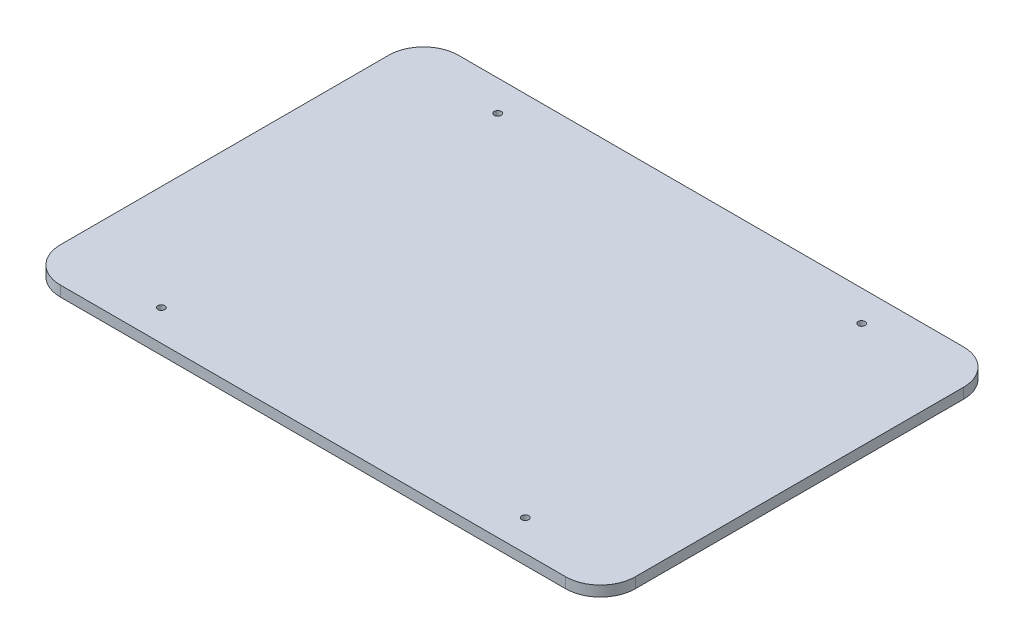
SolidWorks part; units mm, degrees
ref_plane "Front Plane" through (0, 0, 0) normal (0, 0, 1) x (1, 0, 0)
ref_plane "Top Plane" through (0, 0, 0) normal (0, 1, 0) x (1, 0, 0)
ref_plane "Right Plane" through (0, 0, 0) normal (1, 0, 0) x (0, 0, -1)
sketch "Sketch1" plane through (0, 0, 0) normal (0, 1, 0) x (1, 0, 0)
  line L1 (-82.55, 57.15) -> (82.55, 57.15)
  line L2 (-82.55, 57.15) -> (-82.55, -57.15)
  line L3 (-82.55, -57.15) -> (82.55, -57.15)
  line L4 (82.55, 57.15) -> (82.55, -57.15)
  line L5 (-82.55, 57.15) -> (82.55, -57.15) construction
  line L6 (-82.55, -57.15) -> (82.55, 57.15) construction
  point P0 (0, 0)
  dimension "D1" = 165.1
  dimension "D2" = 114.3
extrude "Boss-Extrude1" add sketch "Sketch1" along normal blind 3
fillet "Fillet1" radius 10 4 edges at (82.55, 1.5, 57.15) (82.55, 1.5, -57.15) (-82.55, 1.5, -57.15) (-82.55, 1.5, 57.15)
sketch "Sketch2" plane through (0, 0, 0) normal (0, -1, 0) x (1, 0, 0)
  line L4 (82.55, -47.15) -> (82.55, 47.15)
  line L5 (72.55, 57.15) -> (-72.55, 57.15)
  line L6 (-82.55, 47.15) -> (-82.55, -47.15)
  line L7 (-72.55, -57.15) -> (72.55, -57.15)
  line L8 (82.55, -47.15) -> (82.55, 47.15)
  line L9 (72.55, 57.15) -> (-72.55, 57.15)
  line L10 (-82.55, 47.15) -> (-82.55, -47.15)
  line L11 (-72.55, -57.15) -> (72.55, -57.15)
  circle A0 centre (-52.43, 48.26) radius 1 construction
  circle A1 centre (52.07, 48.26) radius 1 construction
  circle A2 centre (-52.43, -48.34) radius 1 construction
  circle A3 centre (52.07, -48.34) radius 1 construction
  arc A4 (82.55, 47.15) -> (72.55, 57.15) centre (72.55, 47.15) ccw
  arc A5 (-72.55, 57.15) -> (-82.55, 47.15) centre (-72.55, 47.15) ccw
  arc A6 (-82.55, -47.15) -> (-72.55, -57.15) centre (-72.55, -47.15) ccw
  arc A7 (72.55, -57.15) -> (82.55, -47.15) centre (72.55, -47.15) ccw
  arc A8 (82.55, 47.15) -> (72.55, 57.15) centre (72.55, 47.15) ccw
  arc A9 (-72.55, 57.15) -> (-82.55, 47.15) centre (-72.55, 47.15) ccw
  arc A10 (-82.55, -47.15) -> (-72.55, -57.15) centre (-72.55, -47.15) ccw
  arc A11 (72.55, -57.15) -> (82.55, -47.15) centre (72.55, -47.15) ccw
  circle A12 centre (-52.43, 48.26) radius 1
  circle A13 centre (52.07, 48.26) radius 1
  circle A14 centre (-52.43, -48.34) radius 1
  circle A15 centre (52.07, -48.34) radius 1
  circle A16 centre (52.07, 48.26) radius 1
  dimension "D2" = 2
  dimension "D1" = 0
extrude "Cut-Extrude1" cut sketch "Sketch2" against normal through all contours A12 | A14 | A13 | A15
